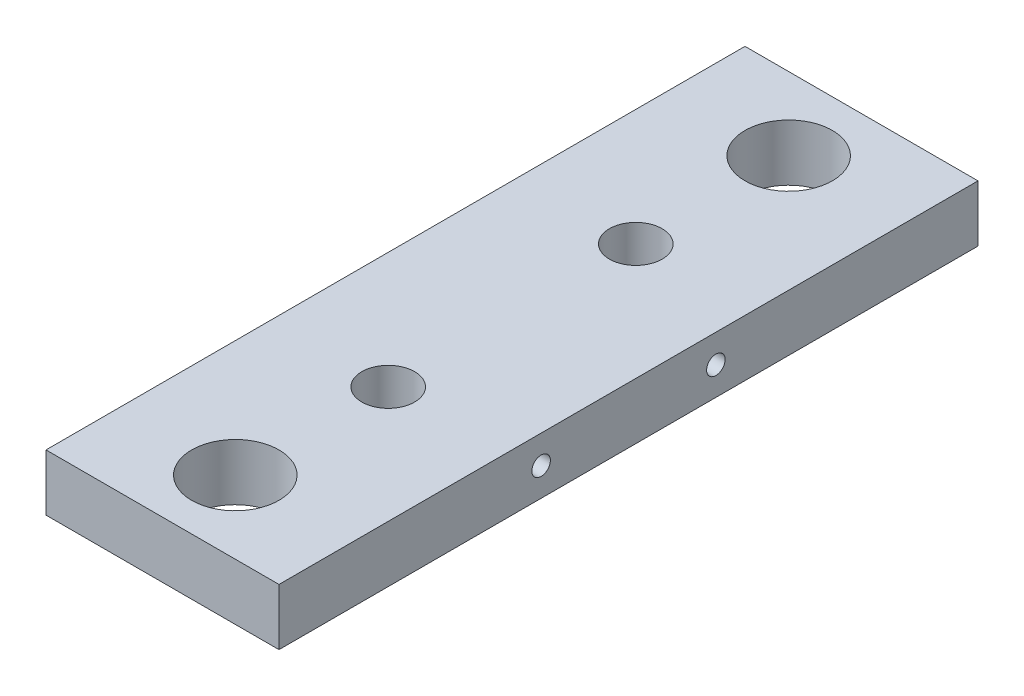
SolidWorks part; units mm, degrees
material "SS 304"
ref_plane "Front Plane" through (0, 0, 0) normal (0, 0, 1) x (1, 0, 0)
ref_plane "Top Plane" through (0, 0, 0) normal (0, 1, 0) x (1, 0, 0)
ref_plane "Right Plane" through (0, 0, 0) normal (1, 0, 0) x (0, 0, -1)
sketch "Sketch1" plane through (0, 0, 0) normal (0, 1, 0) x (1, 0, 0)
  line L0 (-25.4, 76.2) -> (25.4, -76.2) construction
  line L1 (-25.4, 76.2) -> (25.4, 76.2)
  line L2 (-25.4, 76.2) -> (-25.4, -76.2)
  line L3 (-25.4, -76.2) -> (25.4, -76.2)
  line L4 (25.4, 76.2) -> (25.4, -76.2)
  dimension "D1" = 50.8
  dimension "D2" = 152.4
extrude "Extrude1" add sketch "Sketch1" along normal mid plane 12.319
sketch "Sketch2" plane through (0, 6.1595, 0) normal (0, 1, 0) x (-1, 0, 0)
  line L0 (25.4, -76.2) -> (25.4, 76.2) construction
  circle A2 centre (0, -60.325) radius 9.525
  circle A3 centre (0, 60.325) radius 9.525
  dimension "D2" = 60.325
  dimension "D8" = 19.05
  dimension "D1" = 120.65
  dimension "D7" = 25.4
extrude "Cut-Extrude1" cut sketch "Sketch2" against normal up to next
sketch "Sketch5" plane through (25.4, 0, 0) normal (1, 0, 0) x (0, 0, -1)
  line L0 (-76.2, 6.1595) -> (76.2, 6.1595) construction
  line L1 (-76.2, 6.1595) -> (-76.2, -6.1595) construction
  point P0 (-6.35, -0.1905)
  point P1 (31.75, -0.1905)
  dimension "D1" = 6.35
  dimension "D2" = 69.85
  dimension "D3" = 107.95
hole_wizard "1/2-20 Tapped Hole1" positions "Sketch8" profile "Sketch7" tap size "1/2-20" standard "Ansi Inch" end condition up to next
sketch "Sketch8" plane through (0, 6.1595, 0) normal (0, 1, 0) x (-1, 0, 0)
  line L1 (0, 0) -> (17.7539, 0) construction
  circle A1 centre (0, -60.325) radius 9.525 construction
  point P0 (0, -26.9875)
  point P1 (0, 26.9875)
  dimension "D1" = 0
  dimension "D2" = 53.975
sketch "Sketch7" plane through (0, 6.1595, -26.9875) normal (1, 0, 0) x (0, 0, 1)
  line L0 (0, 0) -> (0, 12.319)
  line L1 (0, 12.319) -> (5.7544, 12.319)
  line L2 (5.7544, 12.319) -> (5.7544, 0)
  line L5 (5.7544, 0) -> (0, 0)
  line L11 (0, -6.35) -> (0, 107.95) construction
  dimension "Thru Tap Drill Dia." = 11.5087
  dimension "Thru Tap Drill Depth" = 12.319
cosmetic thread "Hole Thread1" parameters "D1"=12.319, "D2"=12.7
cosmetic thread "Hole Thread2" parameters "D1"=12.319, "D2"=12.7
hole_wizard "#10-32 Tapped Hole1" positions "Sketch9" profile "Sketch10" tap size "#10-32" standard "ANSI Inch"
sketch "Sketch9" plane through (25.4, 0, 0) normal (1, 0, 0) x (0, 0, -1)
  point P0 (-19.05, 0)
  point P2 (19.05, 0)
  dimension "D1" = 38.1
  dimension "D2" = 19.05
sketch "Sketch10" plane through (25.4, 0, 19.05) normal (0, 1, 0) x (0, 0, -1)
  line L0 (0, 0) -> (0, 14.8277)
  line L1 (0, 14.8277) -> (2.0193, 13.6144)
  line L2 (2.0193, 13.6144) -> (2.0193, 0)
  line L5 (2.0193, 0) -> (0, 0)
  line L10 (0, 14.8277) -> (-2.0193, 13.6144) construction
  line L11 (0, -6.35) -> (0, 107.95) construction
  dimension "Tap Drill Dia." = 4.0386
  dimension "Tap Drill Depth" = 13.6144
  dimension "Drill Angle" = 118
cosmetic thread "Hole Thread3" parameters "D1"=9.652, "D2"=4.826
cosmetic thread "Hole Thread4" parameters "D1"=9.652, "D2"=4.826
mirror "Mirror1" about plane through (0, 0, 0) normal (1, 0, 0) of "#10-32 Tapped Hole1"
